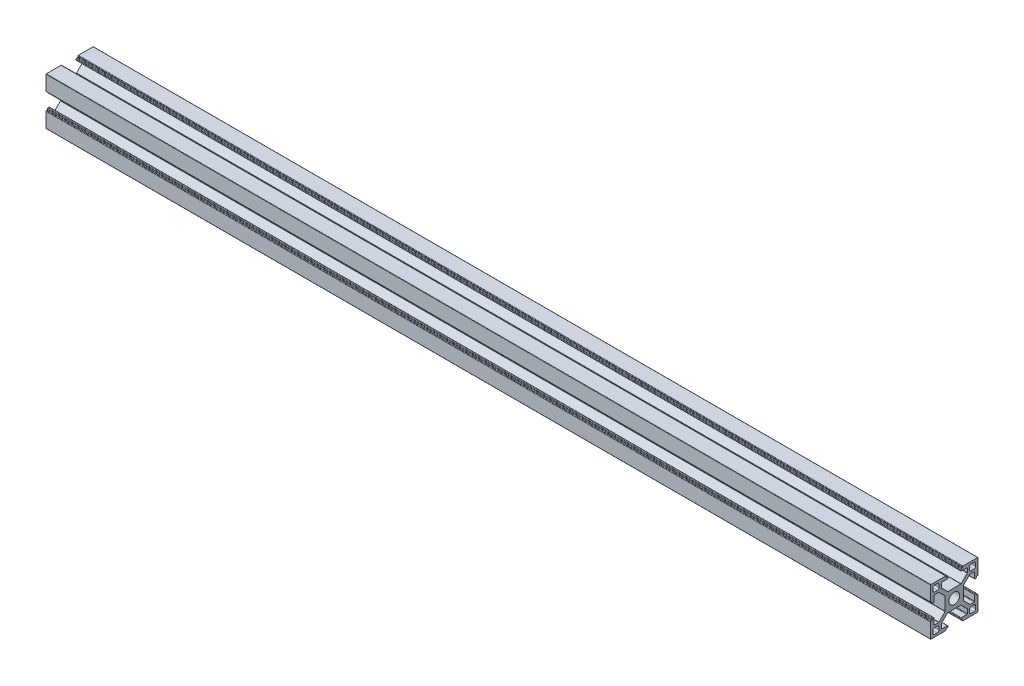
SolidWorks part; units mm, degrees
ref_plane "前视基准面" through (0, 0, 0) normal (0, 0, 1) x (1, 0, 0)
ref_plane "上视基准面" through (0, 0, 0) normal (0, 1, 0) x (1, 0, 0)
ref_plane "右视基准面" through (0, 0, 0) normal (1, 0, 0) x (0, 0, -1)
sketch "草图1" plane through (0, 0, 0) normal (0, 0, 1) x (1, 0, 0)
  line L0 (0, 0) -> (560, 0)
  dimension "D1" = 560
other "3030a 默认<按加工>(1)"
ref_plane "基准面1" through (0, 0, 0) normal (1, 0, 0) x (0, 1, 0)
sketch "草图11" plane through (0, 0, 0) normal (1, 0, 0) x (0, 1, 0)
  line L82 (0, 5.8) -> (-4.1201, 5.8)
  line L83 (-4.3322, 5.8879) -> (-8.1621, 9.7178)
  line L84 (-8.25, 9.9299) -> (-8.25, 12.5)
  line L85 (-7.95, 12.8) -> (-4.4, 12.8)
  line L86 (-4.1, 13.1) -> (-4.1, 13.7)
  line L87 (-4.4, 14) -> (-4.9, 14)
  line L88 (-5.2, 14.3) -> (-5.2, 14.7)
  line L89 (-5.5, 15) -> (-14.8, 15)
  line L90 (-15, 14.8) -> (-15, 5.5)
  line L91 (-14.7, 5.2) -> (-14.3, 5.2)
  line L92 (-14, 4.9) -> (-14, 4.4)
  line L93 (-13.7, 4.1) -> (-13.1, 4.1)
  line L94 (-12.8, 4.4) -> (-12.8, 7.95)
  line L95 (-12.5, 8.25) -> (-9.9299, 8.25)
  line L96 (-9.7178, 8.1621) -> (-5.8879, 4.3322)
  line L97 (-5.8, 4.1201) -> (-5.8, 0)
  line L98 (-5.8, 0) -> (-5.8, -4.1201)
  line L99 (-5.8879, -4.3322) -> (-9.7178, -8.1621)
  line L100 (-9.9299, -8.25) -> (-12.5, -8.25)
  line L101 (-12.8, -7.95) -> (-12.8, -4.4)
  line L102 (-13.1, -4.1) -> (-13.7, -4.1)
  line L103 (-14, -4.4) -> (-14, -4.9)
  line L104 (-14.3, -5.2) -> (-14.7, -5.2)
  line L105 (-15, -5.5) -> (-15, -14.8)
  line L106 (-14.8, -15) -> (-5.5, -15)
  line L107 (-5.2, -14.7) -> (-5.2, -14.3)
  line L108 (-4.9, -14) -> (-4.4, -14)
  line L109 (-4.1, -13.7) -> (-4.1, -13.1)
  line L110 (-4.4, -12.8) -> (-7.95, -12.8)
  line L111 (-8.25, -12.5) -> (-8.25, -9.9299)
  line L112 (-8.1621, -9.7178) -> (-4.3322, -5.8879)
  line L113 (-4.1201, -5.8) -> (0, -5.8)
  line L114 (0, -5.8) -> (4.1201, -5.8)
  line L115 (4.3322, -5.8879) -> (8.1621, -9.7178)
  line L116 (8.25, -9.9299) -> (8.25, -12.5)
  line L117 (7.95, -12.8) -> (4.4, -12.8)
  line L118 (4.1, -13.1) -> (4.1, -13.7)
  line L119 (4.4, -14) -> (4.9, -14)
  line L120 (5.2, -14.3) -> (5.2, -14.7)
  line L121 (5.5, -15) -> (14.8, -15)
  line L122 (15, -14.8) -> (15, -5.5)
  line L123 (14.7, -5.2) -> (14.3, -5.2)
  line L124 (14, -4.9) -> (14, -4.4)
  line L125 (13.7, -4.1) -> (13.1, -4.1)
  line L126 (12.8, -4.4) -> (12.8, -7.95)
  line L127 (12.5, -8.25) -> (9.9299, -8.25)
  line L128 (9.7178, -8.1621) -> (5.8879, -4.3322)
  line L129 (5.8, -4.1201) -> (5.8, 0)
  line L130 (5.8, 0) -> (5.8, 4.1201)
  line L131 (5.8879, 4.3322) -> (9.8056, 8.25)
  line L132 (9.8056, 8.25) -> (12.5, 8.25)
  line L133 (12.8, 7.95) -> (12.8, 4.4)
  line L134 (13.1, 4.1) -> (13.7, 4.1)
  line L135 (14, 4.4) -> (14, 4.9)
  line L136 (14.3, 5.2) -> (14.7, 5.2)
  line L137 (15, 5.5) -> (15, 14.8)
  line L138 (14.8, 15) -> (5.5, 15)
  line L139 (5.2, 14.7) -> (5.2, 14.3)
  line L140 (4.9, 14) -> (4.4, 14)
  line L141 (4.1, 13.7) -> (4.1, 13.1)
  line L142 (4.4, 12.8) -> (7.95, 12.8)
  line L143 (8.25, 12.5) -> (8.25, 9.9299)
  line L144 (8.1621, 9.7178) -> (4.3322, 5.8879)
  line L145 (4.1201, 5.8) -> (0, 5.8)
  line L146 (-10.75, -13.5) -> (-12.5, -13.5)
  line L147 (-13.5, -12.5) -> (-13.5, -10.75)
  line L148 (-12.5, -9.75) -> (-10.75, -9.75)
  line L149 (-9.75, -10.75) -> (-9.75, -12.5)
  line L150 (10.75, -13.5) -> (12.5, -13.5)
  line L151 (13.5, -12.5) -> (13.5, -10.75)
  line L152 (12.5, -9.75) -> (10.75, -9.75)
  line L153 (9.75, -10.75) -> (9.75, -12.5)
  line L154 (-10.75, 13.5) -> (-12.5, 13.5)
  line L155 (-13.5, 12.5) -> (-13.5, 10.75)
  line L156 (-12.5, 9.75) -> (-10.75, 9.75)
  line L157 (-9.75, 10.75) -> (-9.75, 12.5)
  line L158 (10.75, 13.5) -> (12.5, 13.5)
  line L159 (13.5, 12.5) -> (13.5, 10.75)
  line L160 (12.5, 9.75) -> (10.75, 9.75)
  line L161 (9.75, 10.75) -> (9.75, 12.5)
  circle A76 centre (0, 0) radius 3.4
  arc A77 (-4.3322, 5.8879) -> (-4.1201, 5.8) centre (-4.1201, 6.1) ccw
  arc A78 (-8.25, 9.9299) -> (-8.1621, 9.7178) centre (-7.95, 9.9299) ccw
  arc A79 (-7.95, 12.8) -> (-8.25, 12.5) centre (-7.95, 12.5) ccw
  arc A80 (-4.4, 12.8) -> (-4.1, 13.1) centre (-4.4, 13.1) ccw
  arc A81 (-4.1, 13.7) -> (-4.4, 14) centre (-4.4, 13.7) ccw
  arc A82 (-5.2, 14.3) -> (-4.9, 14) centre (-4.9, 14.3) ccw
  arc A83 (-5.2, 14.7) -> (-5.5, 15) centre (-5.5, 14.7) ccw
  arc A84 (-14.8, 15) -> (-15, 14.8) centre (-14.8, 14.8) ccw
  arc A85 (-15, 5.5) -> (-14.7, 5.2) centre (-14.7, 5.5) ccw
  arc A86 (-14, 4.9) -> (-14.3, 5.2) centre (-14.3, 4.9) ccw
  arc A87 (-14, 4.4) -> (-13.7, 4.1) centre (-13.7, 4.4) ccw
  arc A88 (-13.1, 4.1) -> (-12.8, 4.4) centre (-13.1, 4.4) ccw
  arc A89 (-12.5, 8.25) -> (-12.8, 7.95) centre (-12.5, 7.95) ccw
  arc A90 (-9.7178, 8.1621) -> (-9.9299, 8.25) centre (-9.9299, 7.95) ccw
  arc A91 (-5.8, 4.1201) -> (-5.8879, 4.3322) centre (-6.1, 4.1201) ccw
  arc A92 (-5.8879, -4.3322) -> (-5.8, -4.1201) centre (-6.1, -4.1201) ccw
  arc A93 (-9.9299, -8.25) -> (-9.7178, -8.1621) centre (-9.9299, -7.95) ccw
  arc A94 (-12.8, -7.95) -> (-12.5, -8.25) centre (-12.5, -7.95) ccw
  arc A95 (-12.8, -4.4) -> (-13.1, -4.1) centre (-13.1, -4.4) ccw
  arc A96 (-13.7, -4.1) -> (-14, -4.4) centre (-13.7, -4.4) ccw
  arc A97 (-14.3, -5.2) -> (-14, -4.9) centre (-14.3, -4.9) ccw
  arc A98 (-14.7, -5.2) -> (-15, -5.5) centre (-14.7, -5.5) ccw
  arc A99 (-15, -14.8) -> (-14.8, -15) centre (-14.8, -14.8) ccw
  arc A100 (-5.5, -15) -> (-5.2, -14.7) centre (-5.5, -14.7) ccw
  arc A101 (-4.9, -14) -> (-5.2, -14.3) centre (-4.9, -14.3) ccw
  arc A102 (-4.4, -14) -> (-4.1, -13.7) centre (-4.4, -13.7) ccw
  arc A103 (-4.1, -13.1) -> (-4.4, -12.8) centre (-4.4, -13.1) ccw
  arc A104 (-8.25, -12.5) -> (-7.95, -12.8) centre (-7.95, -12.5) ccw
  arc A105 (-8.1621, -9.7178) -> (-8.25, -9.9299) centre (-7.95, -9.9299) ccw
  arc A106 (-4.1201, -5.8) -> (-4.3322, -5.8879) centre (-4.1201, -6.1) ccw
  arc A107 (4.3322, -5.8879) -> (4.1201, -5.8) centre (4.1201, -6.1) ccw
  arc A108 (8.25, -9.9299) -> (8.1621, -9.7178) centre (7.95, -9.9299) ccw
  arc A109 (7.95, -12.8) -> (8.25, -12.5) centre (7.95, -12.5) ccw
  arc A110 (4.4, -12.8) -> (4.1, -13.1) centre (4.4, -13.1) ccw
  arc A111 (4.1, -13.7) -> (4.4, -14) centre (4.4, -13.7) ccw
  arc A112 (5.2, -14.3) -> (4.9, -14) centre (4.9, -14.3) ccw
  arc A113 (5.2, -14.7) -> (5.5, -15) centre (5.5, -14.7) ccw
  arc A114 (14.8, -15) -> (15, -14.8) centre (14.8, -14.8) ccw
  arc A115 (15, -5.5) -> (14.7, -5.2) centre (14.7, -5.5) ccw
  arc A116 (14, -4.9) -> (14.3, -5.2) centre (14.3, -4.9) ccw
  arc A117 (14, -4.4) -> (13.7, -4.1) centre (13.7, -4.4) ccw
  arc A118 (13.1, -4.1) -> (12.8, -4.4) centre (13.1, -4.4) ccw
  arc A119 (12.5, -8.25) -> (12.8, -7.95) centre (12.5, -7.95) ccw
  arc A120 (9.7178, -8.1621) -> (9.9299, -8.25) centre (9.9299, -7.95) ccw
  arc A121 (5.8, -4.1201) -> (5.8879, -4.3322) centre (6.1, -4.1201) ccw
  arc A122 (5.8879, 4.3322) -> (5.8, 4.1201) centre (6.1, 4.1201) ccw
  arc A123 (12.8, 7.95) -> (12.5, 8.25) centre (12.5, 7.95) ccw
  arc A124 (12.8, 4.4) -> (13.1, 4.1) centre (13.1, 4.4) ccw
  arc A125 (13.7, 4.1) -> (14, 4.4) centre (13.7, 4.4) ccw
  arc A126 (14.3, 5.2) -> (14, 4.9) centre (14.3, 4.9) ccw
  arc A127 (14.7, 5.2) -> (15, 5.5) centre (14.7, 5.5) ccw
  arc A128 (15, 14.8) -> (14.8, 15) centre (14.8, 14.8) ccw
  arc A129 (5.5, 15) -> (5.2, 14.7) centre (5.5, 14.7) ccw
  arc A130 (4.9, 14) -> (5.2, 14.3) centre (4.9, 14.3) ccw
  arc A131 (4.4, 14) -> (4.1, 13.7) centre (4.4, 13.7) ccw
  arc A132 (4.1, 13.1) -> (4.4, 12.8) centre (4.4, 13.1) ccw
  arc A133 (8.25, 12.5) -> (7.95, 12.8) centre (7.95, 12.5) ccw
  arc A134 (8.1621, 9.7178) -> (8.25, 9.9299) centre (7.95, 9.9299) ccw
  arc A135 (4.1201, 5.8) -> (4.3322, 5.8879) centre (4.1201, 6.1) ccw
  arc A136 (-10.75, -13.5) -> (-9.75, -12.5) centre (-10.75, -12.5) ccw
  arc A137 (-13.5, -12.5) -> (-12.5, -13.5) centre (-12.5, -12.5) ccw
  arc A138 (-12.5, -9.75) -> (-13.5, -10.75) centre (-12.5, -10.75) ccw
  arc A139 (-9.75, -10.75) -> (-10.75, -9.75) centre (-10.75, -10.75) ccw
  arc A140 (9.75, -12.5) -> (10.75, -13.5) centre (10.75, -12.5) ccw
  arc A141 (12.5, -13.5) -> (13.5, -12.5) centre (12.5, -12.5) ccw
  arc A142 (13.5, -10.75) -> (12.5, -9.75) centre (12.5, -10.75) ccw
  arc A143 (10.75, -9.75) -> (9.75, -10.75) centre (10.75, -10.75) ccw
  arc A144 (-9.75, 12.5) -> (-10.75, 13.5) centre (-10.75, 12.5) ccw
  arc A145 (-12.5, 13.5) -> (-13.5, 12.5) centre (-12.5, 12.5) ccw
  arc A146 (-13.5, 10.75) -> (-12.5, 9.75) centre (-12.5, 10.75) ccw
  arc A147 (-10.75, 9.75) -> (-9.75, 10.75) centre (-10.75, 10.75) ccw
  arc A148 (10.75, 13.5) -> (9.75, 12.5) centre (10.75, 12.5) ccw
  arc A149 (13.5, 12.5) -> (12.5, 13.5) centre (12.5, 12.5) ccw
  arc A150 (12.5, 9.75) -> (13.5, 10.75) centre (12.5, 10.75) ccw
  arc A151 (9.75, 10.75) -> (10.75, 9.75) centre (10.75, 10.75) ccw
  point P0 (0, 0)
